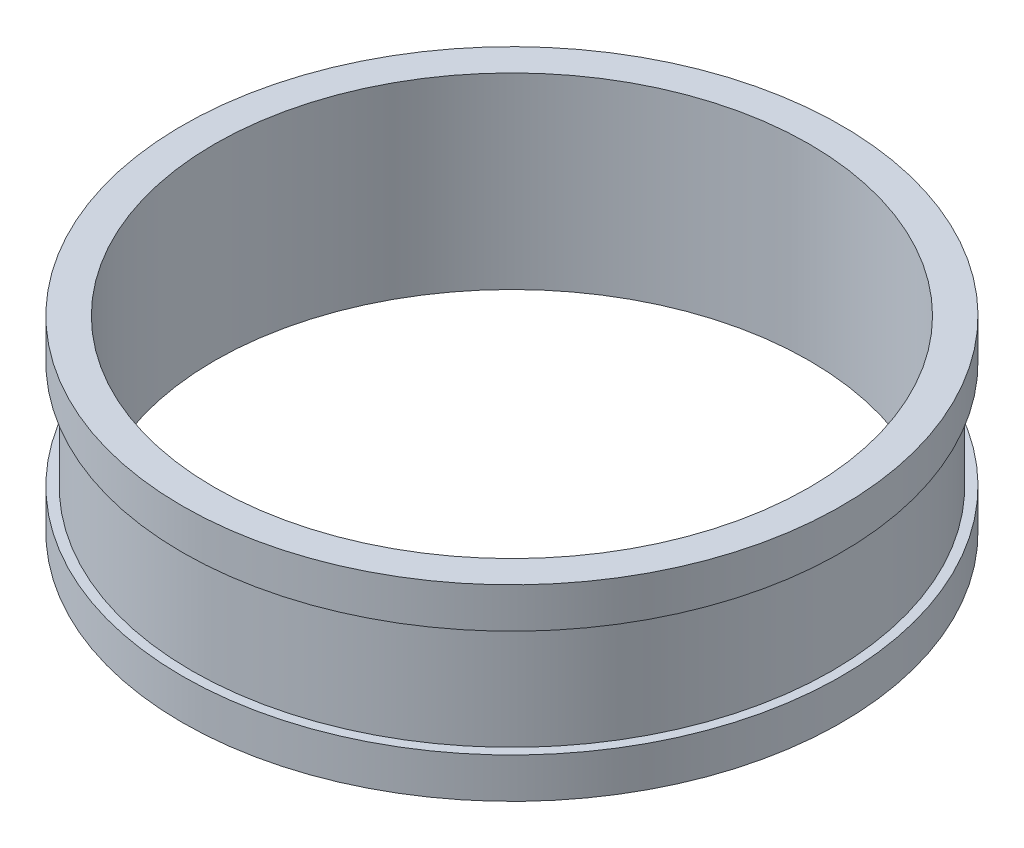
SolidWorks part; units mm, degrees
ref_plane "Front Plane" through (0, 0, 0) normal (0, 0, 1) x (1, 0, 0)
ref_plane "Top Plane" through (0, 0, 0) normal (0, 1, 0) x (1, 0, 0)
ref_plane "Right Plane" through (0, 0, 0) normal (1, 0, 0) x (0, 0, -1)
sketch "Sketch1" plane through (0, 0, 0) normal (0, 1, 0) x (1, 0, 0)
  circle A0 centre (0, 0) radius 11.1
  circle A1 centre (0, 0) radius 12.3
  dimension "D1" = 22.2
  dimension "D2" = 1.2
extrude "Boss-Extrude1" add sketch "Sketch1" along normal blind 7
ref_axis "Axis1" through (0, 7, 0) along (0, -1, 0)
sketch "Sketch2" plane through (0, 0, 0) normal (0, 0, 1) x (1, 0, 0)
  line L0 (-12.3, 7) -> (-12.3, 0) construction
  line L1 (-12.3, 5.5) -> (-11.95, 5.5)
  line L2 (-12.3, 5.5) -> (-12.3, 1.5)
  line L3 (-12.3, 1.5) -> (-11.95, 1.5)
  line L4 (-11.95, 5.5) -> (-11.95, 1.5)
  line L5 (12.3, 7) -> (-12.3, 7) construction
  point P6 (-12.3, 3.5)
  point P7 (-11.95, 3.5)
  dimension "D1" = 4
  dimension "D2" = 0.35
  dimension "D3" = 1.5
revolve "Cut-Revolve1" cut sketch "Sketch2" angle 360 about axis through (0, 7, 0) along (0, -1, 0)
